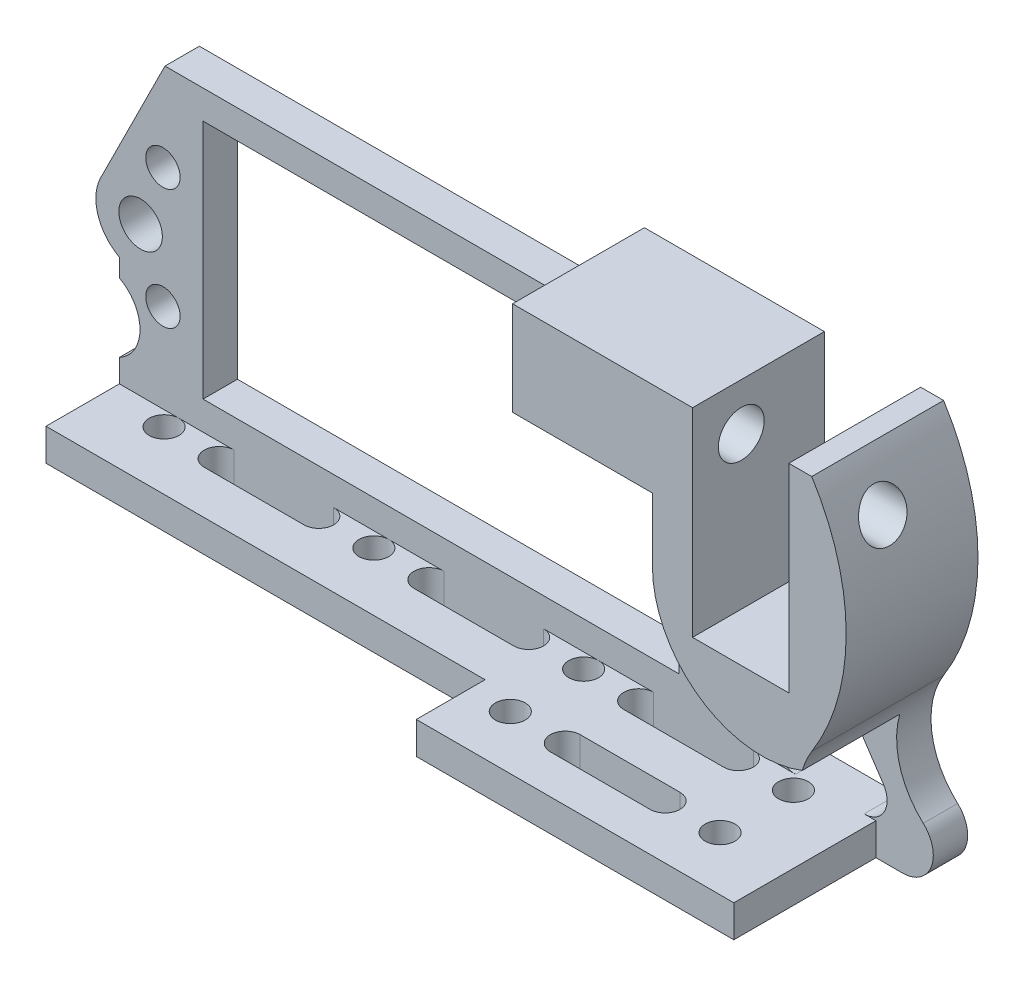
SolidWorks part; units mm, degrees
material "1060 Alloy"
ref_plane "Front" through (0, 0, 0) normal (0, 0, 1) x (1, 0, 0)
ref_plane "Top" through (0, 0, 0) normal (0, 1, 0) x (1, 0, 0)
ref_plane "Right" through (0, 0, 0) normal (1, 0, 0) x (0, 0, -1)
sketch "Sketch1" plane through (0, 0, 0) normal (0, 0, 1) x (1, 0, 0)
  line L0 (-3.3214, 23.5) -> (33.5, 23.5)
  line L1 (0, 0) -> (41.5, 0)
  line L2 (0, 0) -> (0, 21)
  line L3 (0, 21) -> (41.5, 21)
  line L4 (41.5, 0) -> (41.5, 21)
  line L5 (35.5, 25.5) -> (35.5, 29.2)
  line L6 (35.5, 29.2) -> (51.2, 29.2)
  line L7 (51.2, 29.2) -> (51.2, 11.85)
  line L8 (51.2, 11.85) -> (59.6, 11.85)
  line L9 (59.6, 11.85) -> (59.6, 29.2)
  line L10 (59.6, 29.2) -> (61.5988, 29.2)
  line L11 (61.0181, -5.3) -> (-7.3, -5.3)
  line L13 (-7.3, 5.5) -> (-7.3, 7.0674)
  line L14 (-8.9385, 12.2411) -> (-3.3214, 23.5)
  line L15 (49.9615, 0.5177) -> (52.7682, 5.2661)
  line L16 (56.1516, 5.3615) -> (59.3323, 0.6131)
  line L17 (57.6707, -2.5) -> (51.6832, -2.5)
  line L18 (-7.3, -0.5) -> (-7.3, -5.3)
  line L19 (-5.4487, 10.5) -> (0, 10.5) construction
  line L20 (57.3169, 3.6218) -> (48.1778, -2.5) construction
  line L21 (20.75, 21) -> (20.75, 0) construction
  line L22 (54.3842, 8) -> (54.3842, -2.5) construction
  arc A0 (61.5988, 29.2) -> (61.5988, 8.4316) centre (45.1348, 18.8158) cw
  arc A1 (61.5988, 8.4316) -> (62.825, -0.6363) centre (67.6264, 4.6298) ccw
  arc A2 (62.825, -0.6363) -> (61.0181, -5.3) centre (61.0181, -2.6181) cw
  arc A4 (-7.3, 7.0674) -> (-8.9385, 12.2411) centre (-5.4487, 10.5) cw
  arc A5 (-7.3, 5.5) -> (-7.3, -0.5) centre (-8.9, 2.5) cw
  circle A6 centre (-3.5, 15.75) radius 1.5
  circle A7 centre (-5.4487, 10.5) radius 1.9
  circle A8 centre (-3.5, 5.25) radius 1.5
  circle A11 centre (45, 5.25) radius 1.5
  circle A12 centre (45, 15.75) radius 1.5
  arc A13 (59.3323, 0.6131) -> (57.6707, -2.5) centre (57.6707, -0.5) cw
  arc A14 (49.9615, 0.5177) -> (51.6832, -2.5) centre (51.6832, -0.5) ccw
  arc A15 (52.7682, 5.2661) -> (56.1516, 5.3615) centre (54.4899, 4.2484) cw
  arc A16 (35.5, 25.5) -> (33.5, 23.5) centre (33.5, 25.5) cw
  point P31 (64.6, 18.8158)
  point P33 (0, 10.5)
  dimension "D12" = 6
  dimension "D14" = 2
  dimension "D15" = 3
  dimension "D16" = 7.5
  dimension "D17" = 2.2
  dimension "D18" = 3.8
  dimension "D19" = 2
  dimension "D10" = 1.8
  dimension "D28" = 2
  dimension "D29" = 2
  dimension "D1" = 41.5
  dimension "D2" = 21
  dimension "D3" = 2.5
  dimension "D4" = 5.3
  dimension "D5" = 8.4
  dimension "D6" = 15.7
  dimension "D7" = 5
  dimension "D8" = 17.35
  dimension "D9" = 5.5
  dimension "D11" = 4.8
  dimension "D13" = 7.3
  dimension "D20" = 6
  dimension "D21" = 5.7
  dimension "D22" = 71
  dimension "D23" = 19
  dimension "D24" = 2.8
  dimension "D25" = 2
  dimension "D26" = 11
  dimension "D27" = 10.5
extrude "Boss-Extrude1" add sketch "Sketch1" along normal blind 3
sketch "Sketch2" plane through (0, 0, 3) normal (0, 0, 1) x (1, 0, 0)
  line L0 (61.5988, 29.2) -> (59.6, 29.2) construction
  line L1 (59.6, 29.2) -> (59.6, 11.85) construction
  line L2 (51.2, 11.85) -> (51.2, 29.2) construction
  line L3 (51.2, 29.2) -> (35.5, 29.2) construction
  line L4 (61.5988, 29.2) -> (59.6, 29.2)
  line L5 (59.6, 29.2) -> (59.6, 11.85)
  line L6 (51.2, 11.85) -> (51.2, 29.2)
  line L7 (51.2, 29.2) -> (35.5, 29.2)
  line L8 (35.5, 29.2) -> (35.5, 21)
  line L9 (41.5, 21) -> (0, 21) construction
  line L10 (35.5, 21) -> (47.7, 21)
  line L11 (47.7, 21) -> (47.7, 15.4724)
  line L12 (51.2, 11.85) -> (59.6, 11.85)
  arc A0 (61.5988, 8.4316) -> (62.825, -0.6363) centre (67.6264, 4.6298) ccw construction
  arc A1 (61.5988, 8.4316) -> (61.5988, 29.2) centre (45.1348, 18.8158) ccw construction
  arc A2 (61.5988, 8.4316) -> (60.7718, 6.5793) centre (67.6264, 4.6298) ccw
  arc A3 (61.5988, 8.4316) -> (61.5988, 29.2) centre (45.1348, 18.8158) ccw
  arc A4 (47.7, 15.4724) -> (60.7718, 6.5793) centre (57.261, 15.4724) ccw
  arc A5 (56.1516, 5.3615) -> (52.7682, 5.2661) centre (54.4899, 4.2484) ccw construction
  dimension "D1" = 2.5
  dimension "D2" = 3.5
extrude "Boss-Extrude2" add sketch "Sketch2" along normal blind 8.5
sketch "Sketch3" plane through (0, 0, 3) normal (0, 0, 1) x (1, 0, 0)
  line L0 (46.3968, -5.3) -> (-7.3, -5.3)
  line L1 (-7.3, -5.3) -> (61.0181, -5.3) construction
  line L2 (-7.3, -5.3) -> (-7.3, -2.5)
  line L4 (-7.3, -2.5) -> (58.7, -2.5)
  line L5 (51.6832, -2.5) -> (57.6707, -2.5) construction
  line L6 (58.7, -2.5) -> (58.7, -5.3)
  line L7 (58.7, -5.3) -> (46.3968, -5.3)
  dimension "D1" = 66
extrude "Boss-Extrude3" add sketch "Sketch3" along normal blind 12.4
sketch "Sketch4" plane through (0, -2.5, 0) normal (0, 1, 0) x (1, 0, 0)
  line L0 (48, -4.3) -> (39.3, -4.3) construction
  line L1 (48, -5.6) -> (39.3, -5.6)
  line L2 (48, -3) -> (39.3, -3)
  line L3 (51.6832, -3) -> (-7.3, -3) construction
  line L4 (51.6832, -3) -> (-7.3, -3) construction
  line L5 (43.65, -4.3) -> (43.65, -5.6) construction
  line L6 (58.7, -15.4) -> (58.7, -3) construction
  line L7 (48, -10.7) -> (39.3, -10.7) construction
  line L8 (48, -12) -> (39.3, -12)
  line L9 (48, -9.4) -> (39.3, -9.4)
  line L10 (29.7, -10.7) -> (21, -10.7) construction
  line L11 (29.7, -12) -> (21, -12)
  line L12 (29.7, -9.4) -> (21, -9.4)
  line L13 (11.4, -10.7) -> (2.7, -10.7) construction
  line L14 (11.4, -12) -> (2.7, -12)
  line L15 (11.4, -9.4) -> (2.7, -9.4)
  line L16 (29.7, -4.3) -> (21, -4.3) construction
  line L17 (29.7, -5.6) -> (21, -5.6)
  line L18 (29.7, -3) -> (21, -3)
  line L19 (11.4, -4.3) -> (2.7, -4.3) construction
  line L20 (11.4, -5.6) -> (2.7, -5.6)
  line L21 (11.4, -3) -> (2.7, -3)
  arc A0 (48, -5.6) -> (48, -3) centre (48, -4.3) ccw
  arc A1 (39.3, -3) -> (39.3, -5.6) centre (39.3, -4.3) ccw
  circle A2 centre (52.8, -4.3) radius 1.3
  circle A3 centre (34.5, -4.3) radius 1.3
  circle A4 centre (52.8, -10.7) radius 1.3
  circle A5 centre (34.5, -10.7) radius 1.3
  arc A6 (48, -12) -> (48, -9.4) centre (48, -10.7) ccw
  arc A7 (39.3, -9.4) -> (39.3, -12) centre (39.3, -10.7) ccw
  circle A8 centre (34.5, -10.7) radius 1.3
  circle A9 centre (16.2, -10.7) radius 1.3
  arc A10 (29.7, -12) -> (29.7, -9.4) centre (29.7, -10.7) ccw
  arc A11 (21, -9.4) -> (21, -12) centre (21, -10.7) ccw
  circle A12 centre (16.2, -10.7) radius 1.3
  circle A13 centre (-2.1, -10.7) radius 1.3
  arc A14 (11.4, -12) -> (11.4, -9.4) centre (11.4, -10.7) ccw
  arc A15 (2.7, -9.4) -> (2.7, -12) centre (2.7, -10.7) ccw
  circle A16 centre (34.5, -4.3) radius 1.3
  circle A17 centre (16.2, -4.3) radius 1.3
  arc A18 (29.7, -5.6) -> (29.7, -3) centre (29.7, -4.3) ccw
  arc A19 (21, -3) -> (21, -5.6) centre (21, -4.3) ccw
  circle A20 centre (16.2, -4.3) radius 1.3
  circle A21 centre (-2.1, -4.3) radius 1.3
  arc A22 (11.4, -5.6) -> (11.4, -3) centre (11.4, -4.3) ccw
  arc A23 (2.7, -3) -> (2.7, -5.6) centre (2.7, -4.3) ccw
  point P2 (43.65, -4.3)
  point P9 (43.65, -3)
  point P22 (43.65, -10.7)
  point P33 (25.35, -10.7)
  point P44 (7.05, -10.7)
  point P55 (25.35, -4.3)
  point P66 (7.05, -4.3)
  dimension "D1" = 11.3
  dimension "D3" = 2.2
  dimension "D2" = 2.6
  dimension "D4" = 4.6
  dimension "D5" = 2
  dimension "D6" = 3
extrude "Cut-Extrude1" cut sketch "Sketch4" against normal blind 12.4 contours L17 A19 L18 A18 | L1 A1 L2 A0 | A3 | A4 | A2 | L9 A7 L8 A6 | A5 | L11 A11 L12 A10 | A9 | A17 | A22 L21 A23 L20 | L15 A15 L14 A14 | A13 | A21
sketch "Sketch5" plane through (0, -2.5, 0) normal (0, 1, 0) x (1, 0, 0)
  line L0 (-7.3, -15.4) -> (-7.3, -3) construction
  line L1 (-7.3, -9.4) -> (31, -9.4)
  line L2 (-7.3, -9.4) -> (-7.3, -15.4)
  line L3 (-7.3, -15.4) -> (31, -15.4)
  line L4 (31, -9.4) -> (31, -15.4)
  line L5 (58.7, -15.4) -> (-7.3, -15.4) construction
  arc A2 (29.7, -12) -> (29.7, -9.4) centre (29.7, -10.7) ccw construction
  arc A3 (29.7, -12) -> (29.7, -9.4) centre (29.7, -10.7) ccw construction
  point P11 (31, -10.7)
  dimension "D1" = 6
extrude "Cut-Extrude2" cut sketch "Sketch5" against normal blind 12.4
sketch "Sketch6" plane through (35.5, 0, 0) normal (-1, 0, 0) x (0, 0, 1)
  line L0 (3, 21) -> (3, 29.2) construction
  line L1 (11.5, 29.2) -> (0, 29.2) construction
  line L2 (11.5, 29.2) -> (11.5, 21) construction
  line L3 (11.5, 21) -> (3, 21) construction
  circle A0 centre (7.25, 25.1) radius 2
  point P10 (11.5, 25.1)
  point P12 (7.25, 21)
  dimension "D1" = 4
extrude "Cut-Extrude3" cut sketch "Sketch6" against normal blind 42.4
